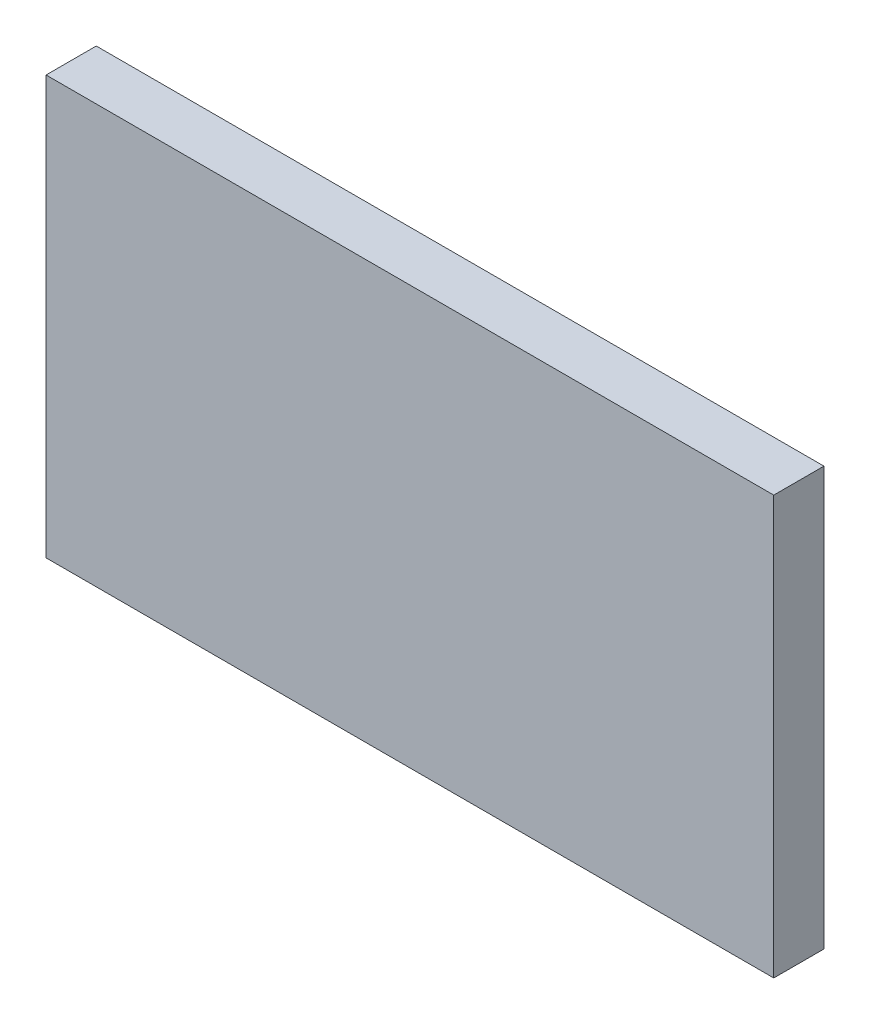
SolidWorks part; units mm, degrees
ref_plane "Alzado" through (0, 0, 0) normal (0, 0, 1) x (1, 0, 0)
ref_plane "Planta" through (0, 0, 0) normal (0, 1, 0) x (1, 0, 0)
ref_plane "Vista lateral" through (0, 0, 0) normal (1, 0, 0) x (0, 0, -1)
sketch "Croquis1" plane through (0, 0, 0) normal (0, 0, 1) x (1, 0, 0)
  line L0 (0, 0) -> (0, 100)
  line L1 (0, 100) -> (174, 100)
  line L2 (174, 100) -> (174, 0)
  line L3 (174, 0) -> (0, 0)
  dimension "D1" = 100
  dimension "D2" = 174
extrude "Saliente-Extruir1" add sketch "Croquis1" along normal blind 12
